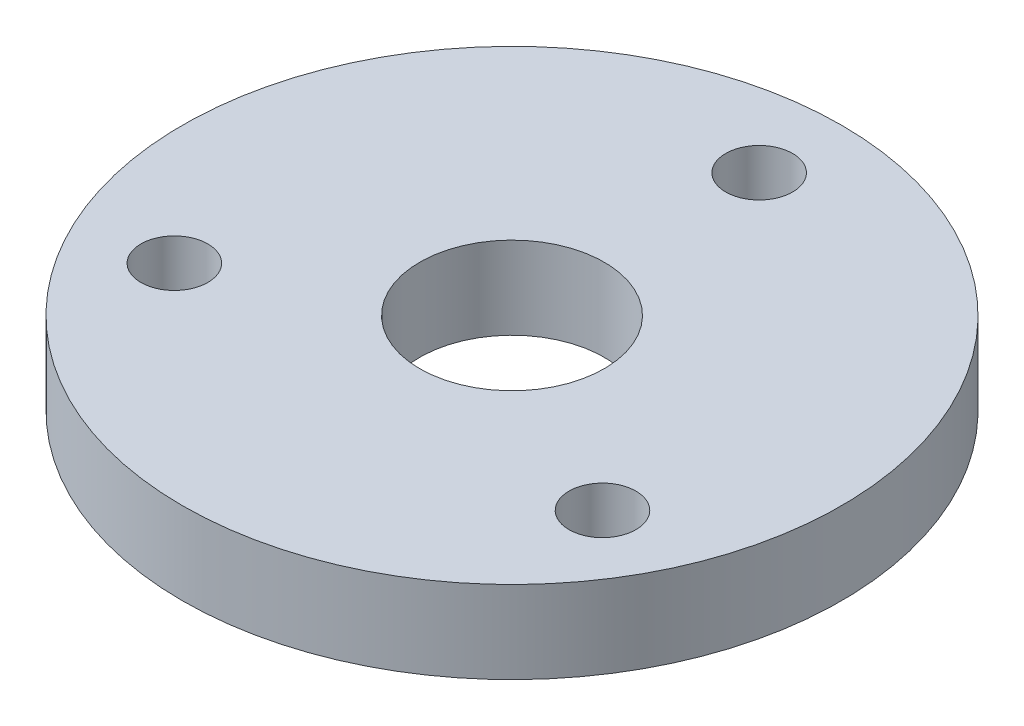
SolidWorks part; units mm, degrees
ref_plane "Front Plane" through (0, 0, 0) normal (0, 0, 1) x (1, 0, 0)
ref_plane "Top Plane" through (0, 0, 0) normal (0, 1, 0) x (1, 0, 0)
ref_plane "Right Plane" through (0, 0, 0) normal (1, 0, 0) x (0, 0, -1)
sketch "Sketch1" plane through (0, 0, 0) normal (0, 1, 0) x (1, 0, 0)
  circle A0 centre (0, 0) radius 100
  circle A1 centre (0, 0) radius 28
  circle A2 centre (0, 75) radius 10.15
  circle A3 centre (64.9519, -37.5) radius 10.15
  circle A4 centre (-64.9519, -37.5) radius 10.15
  point P12 (0, 0)
  dimension "D1" = 200
  dimension "D2" = 56
  dimension "D3" = 20.3
  dimension "D4" = 75
  dimension "D5" = 3
extrude "Boss-Extrude1" add sketch "Sketch1" along normal blind 25
